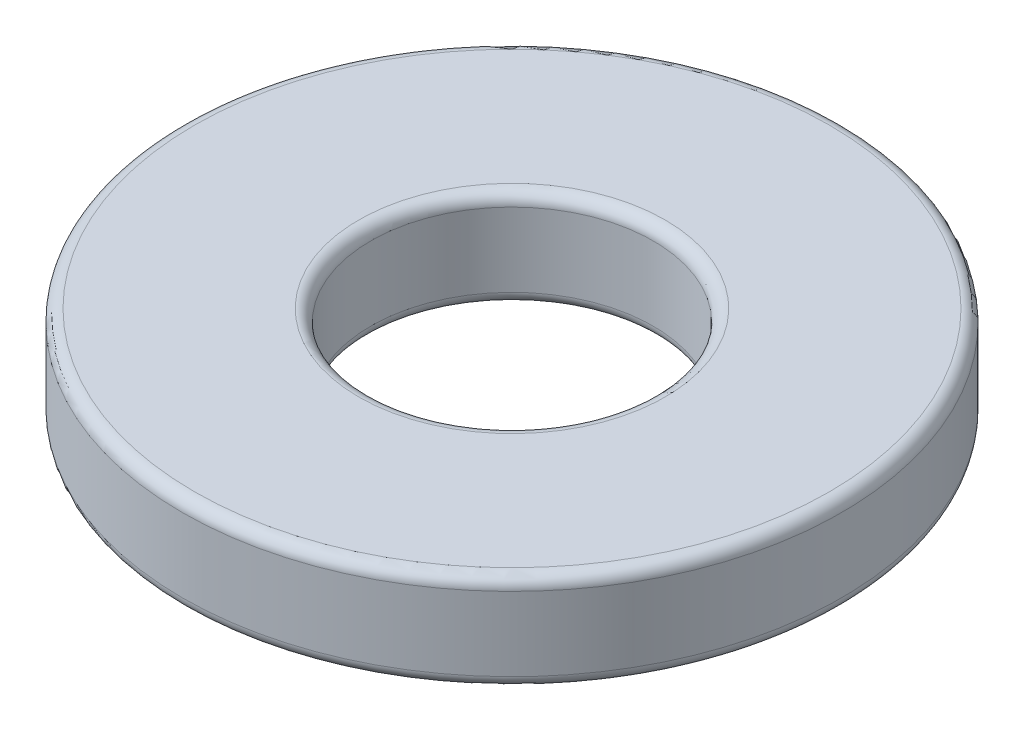
SolidWorks part; units mm, degrees
material "Stainless Steel (ferritic)"
ref_plane "Front Plane" through (0, 0, 0) normal (0, 0, 1) x (1, 0, 0)
ref_plane "Top Plane" through (0, 0, 0) normal (0, 1, 0) x (1, 0, 0)
ref_plane "Right Plane" through (0, 0, 0) normal (1, 0, 0) x (0, 0, -1)
sketch "Sketch1" plane through (0, 0, 0) normal (0, 1, 0) x (1, 0, 0)
  circle A0 centre (0, 0) radius 5.5562
  dimension "OD" = 11.1125
extrude "Boss-Extrude1" add sketch "Sketch1" along normal blind 1.651
sketch "Sketch5" plane through (0, 1.651, 0) normal (0, 1, 0) x (-1, 0, 0)
  circle A0 centre (0, 0) radius 2.3813
  dimension "ID" = 4.7625
extrude "Cut-Extrude1" cut sketch "Sketch5" against normal through all
fillet "Fillet1" radius 0.2032 4 edges at (0, 0, 5.5562) (0, 1.651, 5.5562) (0, 1.651, 2.3813) (0, 0, 2.3813)
